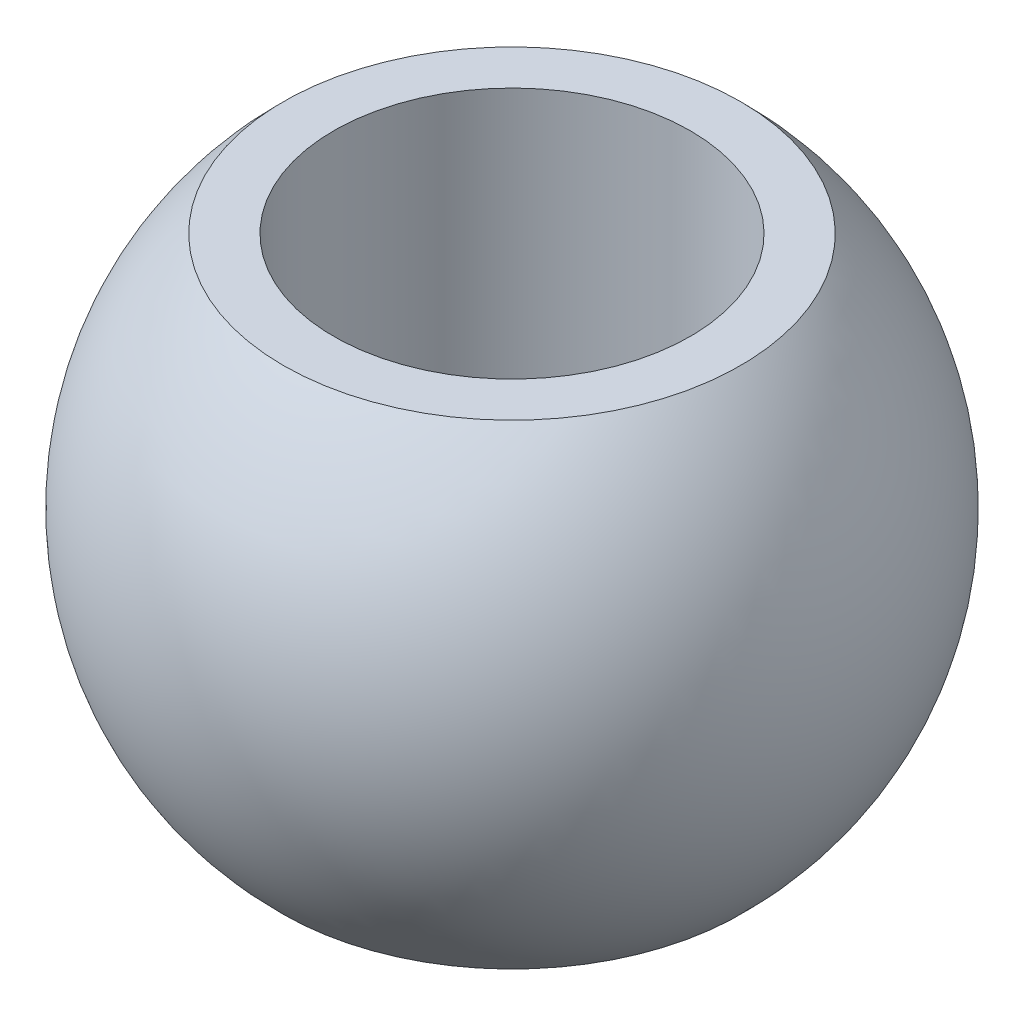
SolidWorks part; units mm, degrees
material "1.0545 (S355N)"
ref_plane "Płaszczyzna przednia" through (0, 0, 0) normal (0, 0, 1) x (1, 0, 0)
ref_plane "Płaszczyzna górna" through (0, 0, 0) normal (0, 1, 0) x (1, 0, 0)
ref_plane "Płaszczyzna prawa" through (0, 0, 0) normal (1, 0, 0) x (0, 0, -1)
sketch "Szkic1" plane through (0, 0, 0) normal (0, 0, 1) x (1, 0, 0)
  line L0 (0, -11.1) -> (0, 11.1) construction
  line L1 (6, -8) -> (6, 8)
  line L2 (6, 8) -> (7.6948, 8)
  line L3 (6, -8) -> (7.6948, -8)
  arc A0 (7.6948, -8) -> (7.6948, 8) centre (0, 0) ccw
  point P6 (6, 0)
  dimension "d3" = 22.2
  dimension "d1" = 6
  dimension "b1" = 16
revolve "Obrót1" add sketch "Szkic1" angle 360 about L0
